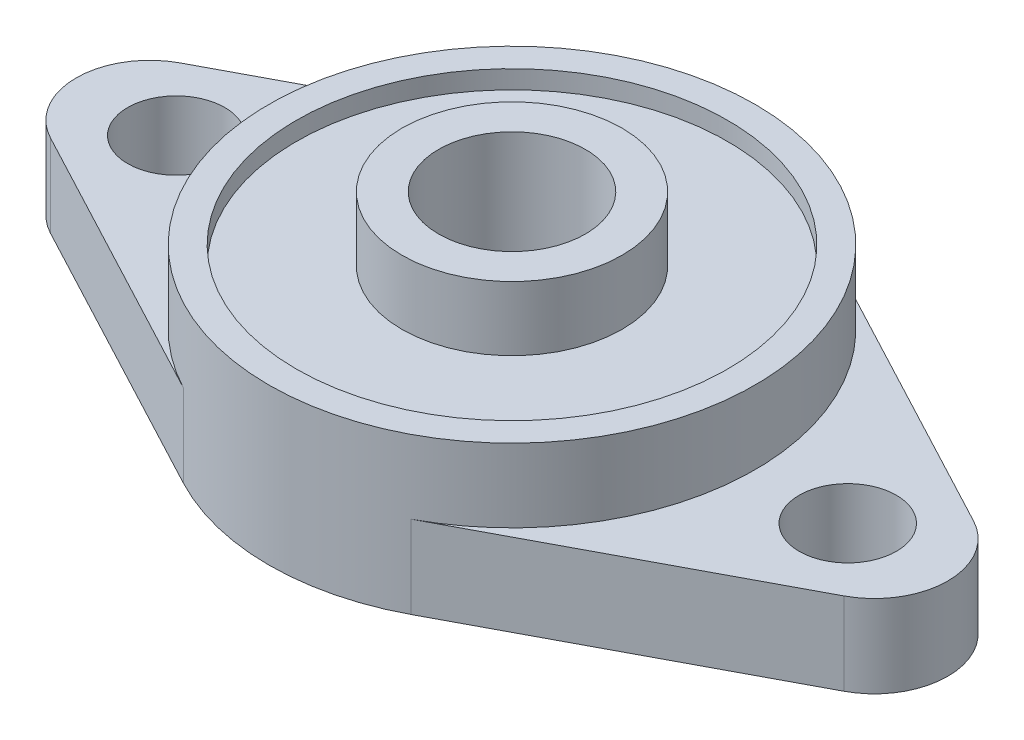
SolidWorks part; units mm, degrees
ref_plane "Front Plane" through (0, 0, 0) normal (0, 0, 1) x (1, 0, 0)
ref_plane "Top Plane" through (0, 0, 0) normal (0, 1, 0) x (1, 0, 0)
ref_plane "Right Plane" through (0, 0, 0) normal (1, 0, 0) x (0, 0, -1)
sketch "Sketch1" plane through (0, 0, 0) normal (0, 1, 0) x (1, 0, 0)
  line L0 (6.2057, 11.7069) -> (21.6234, 3.5342)
  line L1 (6.2057, -11.7069) -> (21.6234, -3.5342)
  line L2 (-6.2057, -11.7069) -> (-21.6234, -3.5342)
  line L3 (-6.2057, 11.7069) -> (-21.6234, 3.5342)
  line L4 (-19.75, 0) -> (0, 0) construction
  line L5 (0, 0) -> (19.75, 0) construction
  circle A0 centre (0, 0) radius 13.25 construction
  arc A1 (-21.6234, 3.5342) -> (-21.6234, -3.5342) centre (-19.75, 0) ccw
  arc A2 (21.6234, 3.5342) -> (21.6234, -3.5342) centre (19.75, 0) cw
  arc A3 (-6.2057, 11.7069) -> (6.2057, 11.7069) centre (0, 0) cw
  arc A4 (-6.2057, -11.7069) -> (6.2057, -11.7069) centre (0, 0) ccw
  circle A5 centre (-18.3, 0) radius 2.65
  circle A6 centre (18.3, 0) radius 2.65
  circle A7 centre (0, 0) radius 4
  point P17 (23.75, 0)
  point P18 (-23.75, 0)
  dimension "D1" = 26.5
  dimension "D3" = 4
  dimension "D4" = 5.3
  dimension "D7" = 8
  dimension "D2" = 47.5
  dimension "D5" = 36.6
  dimension "D6" = 18.3
extrude "Boss-Extrude1" add sketch "Sketch1" along normal blind 4.5
sketch "Sketch2" plane through (0, 4.5, 0) normal (0, 1, 0) x (1, 0, 0)
  circle A0 centre (0, 0) radius 13.25
  arc A1 (6.2057, 11.7069) -> (-6.2057, 11.7069) centre (0, 0) ccw construction
  circle A2 centre (0, 0) radius 4
  circle A3 centre (0, 0) radius 4 construction
extrude "Boss-Extrude2" add sketch "Sketch2" along normal blind 4
sketch "Sketch3" plane through (0, 8.5, 0) normal (0, 1, 0) x (1, 0, 0)
  circle A0 centre (0, 0) radius 4
  circle A1 centre (0, 0) radius 4 construction
  circle A2 centre (0, 0) radius 6
  dimension "D1" = 12
extrude "Boss-Extrude3" add sketch "Sketch3" along normal blind 2.5
sketch "Sketch4" plane through (0, 8.5, 0) normal (0, 1, 0) x (1, 0, 0)
  circle A0 centre (0, 0) radius 6 construction
  circle A1 centre (0, 0) radius 6
  circle A2 centre (0, 0) radius 11.75
  circle A3 centre (0, 0) radius 13.25 construction
  dimension "D1" = 1.5
extrude "Cut-Extrude1" cut sketch "Sketch4" against normal blind 1
